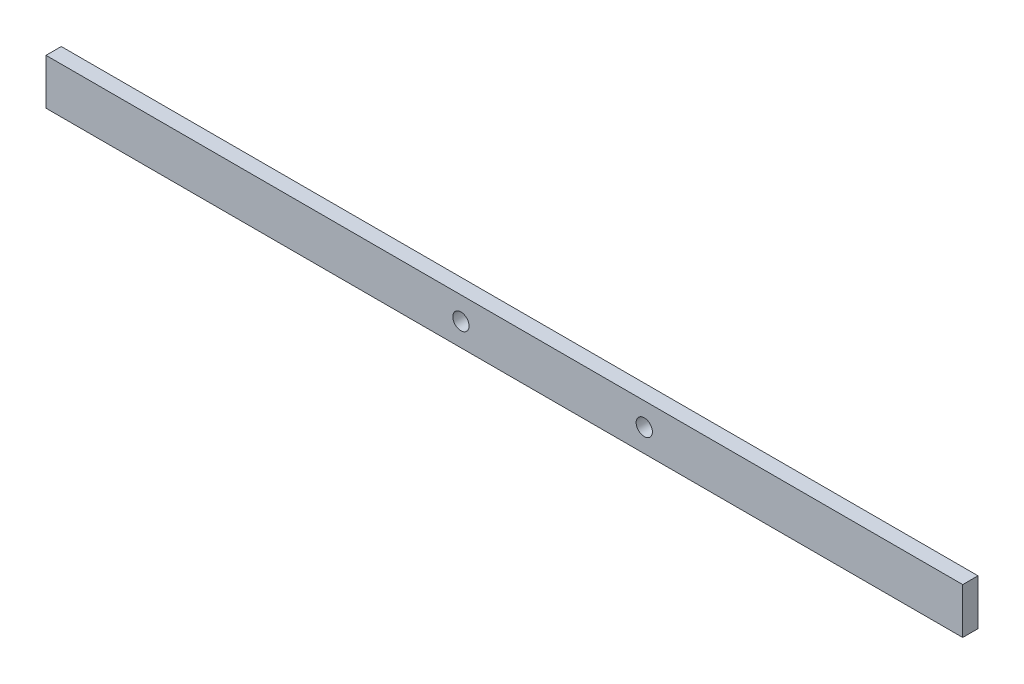
SolidWorks part; units mm, degrees
ref_plane "Front Plane" through (0, 0, 0) normal (0, 0, 1) x (1, 0, 0)
ref_plane "Top Plane" through (0, 0, 0) normal (0, 1, 0) x (1, 0, 0)
ref_plane "Right Plane" through (0, 0, 0) normal (1, 0, 0) x (0, 0, -1)
sketch "Sketch1" plane through (0, 0, 0) normal (0, 0, 1) x (1, 0, 0)
  line L1 (-190.5, -9.525) -> (190.5, -9.525)
  line L2 (-190.5, -9.525) -> (-190.5, 9.525)
  line L3 (-190.5, 9.525) -> (190.5, 9.525)
  line L4 (190.5, -9.525) -> (190.5, 9.525)
  line L5 (-190.5, -9.525) -> (190.5, 9.525) construction
  line L6 (-190.5, 9.525) -> (190.5, -9.525) construction
  point P0 (0, 0)
  dimension "D1" = 381
  dimension "D2" = 19.05
extrude "Boss-Extrude1" add sketch "Sketch1" along normal blind 6.35
hole_wizard "1/4 Clearance Hole1" positions "Sketch2" profile "Sketch3" hole size "1/4" standard "ANSI Inch" end condition through all
sketch "Sketch2" plane through (0, 0, 6.35) normal (0, 0, 1) x (1, 0, 0)
  point P0 (-18.0467, 0)
  point P2 (58.1533, 0)
  dimension "D1" = 18.0467
  dimension "D2" = 76.2
sketch "Sketch3" plane through (-18.0467, 0, 6.35) normal (1, 0, 0) x (0, -1, 0)
  line L0 (0, 0) -> (0, 6.35)
  line L1 (0, 6.35) -> (3.3782, 6.35)
  line L2 (3.3782, 6.35) -> (3.3782, 0)
  line L5 (3.3782, 0) -> (0, 0)
  line L11 (0, -6.35) -> (0, 107.95) construction
  dimension "Thru Hole Dia." = 6.7564
  dimension "Thru Hole Depth" = 6.35
